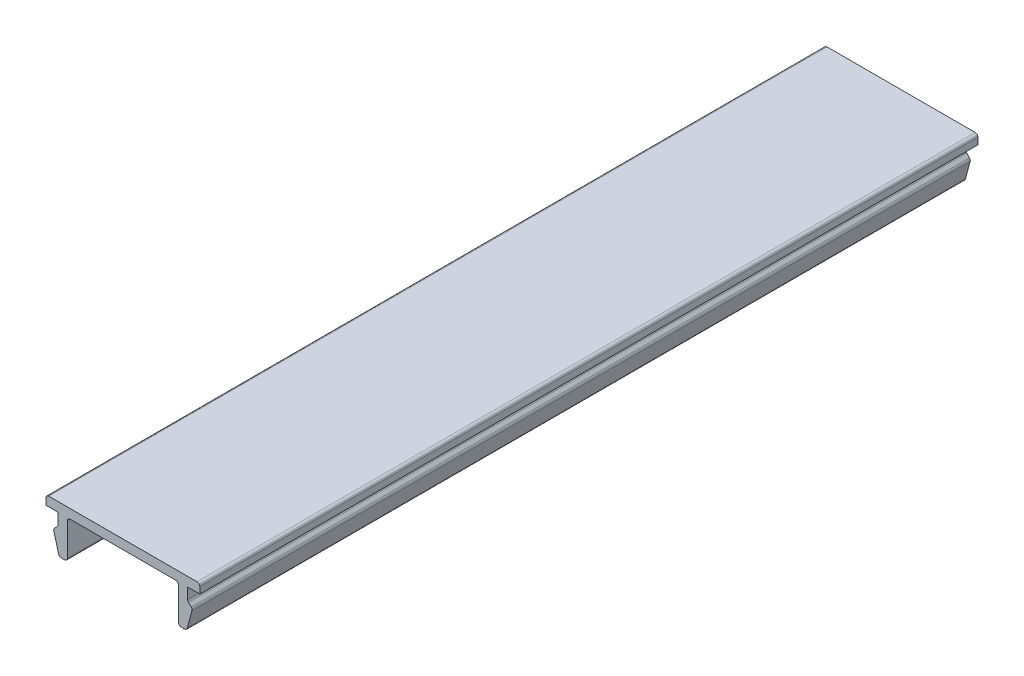
SolidWorks part; units mm, degrees
material "ABS"
ref_plane "Plano frontal" through (0, 0, 0) normal (0, 0, 1) x (1, 0, 0)
ref_plane "Plano superior" through (0, 0, 0) normal (0, 1, 0) x (1, 0, 0)
ref_plane "Plano direito" through (0, 0, 0) normal (1, 0, 0) x (0, 0, -1)
sketch "Sketch1" plane through (0, 0, 0) normal (0, 0, 1) x (1, 0, 0)
  line L0 (-8.3, 1) -> (8.3, 1)
  line L1 (-8.3, 0) -> (-7, 0)
  line L2 (-8.3, 1) -> (-8.3, 0)
  line L3 (8.3, 1) -> (8.3, 0)
  line L4 (-7, 0) -> (-7, -1.3)
  line L5 (-7, -1.3) -> (-7.5, -1.8)
  line L6 (-7.5, -1.8) -> (-6.8837, -4.1)
  line L7 (-6, 0) -> (-6, -4.1)
  line L8 (-6, -4.1) -> (-6.8837, -4.1)
  line L9 (0, 0) -> (0, -1.7195) construction
  line L10 (6, -4.1) -> (6.8837, -4.1)
  line L11 (6, 0) -> (6, -4.1)
  line L12 (7.5, -1.8) -> (6.8837, -4.1)
  line L13 (7, -1.3) -> (7.5, -1.8)
  line L14 (7, 0) -> (7, -1.3)
  line L15 (7, 0) -> (8.3, 0)
  line L16 (-8.3, 0) -> (8.3, 0) construction
  line L17 (-6, 0) -> (6, 0)
  point P21 (0, 1)
  dimension "D1" = 16.6
  dimension "D3" = 1.3
  dimension "D4" = 1.3
  dimension "D5" = 135
  dimension "D6" = 120
  dimension "D7" = 4.1
  dimension "D8" = 0.5
  dimension "D9" = 1
  dimension "D2" = 1
extrude "Boss-Extrude1" add sketch "Sketch1" along normal blind 84
fillet "Fillet1" radius 0.3 12 edges at (8.3, 1, 42) (7, -1.3, 42) (7.5, -1.8, 42) (6.8837, -4.1, 42) (6, -4.1, 42) (6, 0, 42) (-6, 0, 42) (-6, -4.1, 42) (-6.8837, -4.1, 42) (-7.5, -1.8, 42) (-7, -1.3, 42) (-8.3, 1, 42)
